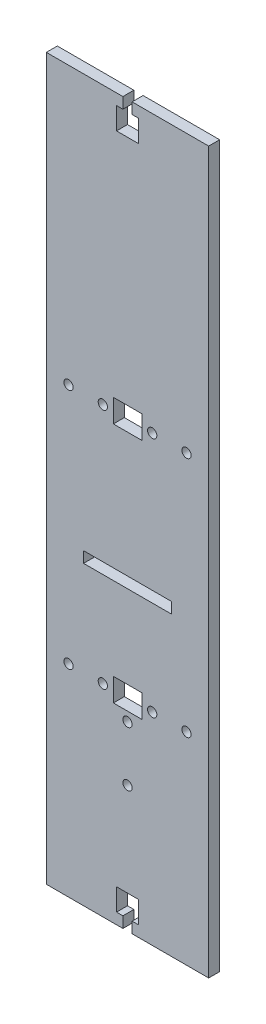
SolidWorks part; units mm, degrees
ref_plane "Front Plane" through (0, 0, 0) normal (0, 0, 1) x (1, 0, 0)
ref_plane "Top Plane" through (0, 0, 0) normal (0, 1, 0) x (1, 0, 0)
ref_plane "Right Plane" through (0, 0, 0) normal (1, 0, 0) x (0, 0, -1)
sketch "Sketch1" plane through (0, 0, 0) normal (0, 0, 1) x (1, 0, 0)
  line L1 (36.95, -164) -> (-36.95, -164)
  line L2 (36.95, -164) -> (36.95, 164)
  line L3 (36.95, 164) -> (-36.95, 164)
  line L4 (-36.95, -164) -> (-36.95, 164)
  line L5 (36.95, -164) -> (-36.95, 164) construction
  line L6 (36.95, 164) -> (-36.95, -164) construction
  point P0 (0, 0)
  dimension "D1" = 328
  dimension "D2" = 73.9
extrude "Boss-Extrude1" add sketch "Sketch1" along normal blind 5
sketch "Sketch2" plane through (0, 0, 5) normal (0, 0, 1) x (1, 0, 0)
  line L0 (-39.8376, -81.5) -> (39.8368, -81.5) construction
  line L1 (-39.8376, -84) -> (-39.8376, -79) construction
  line L2 (39.8368, -84) -> (39.8368, -79) construction
  circle A0 centre (-0.0004, -81.5) radius 2.1
  dimension "D1" = 4.2
extrude "Cut-Extrude1" cut sketch "Sketch2" against normal blind 10
sketch "Sketch3" plane through (0, 0, 5) normal (0, 0, 1) x (1, 0, 0)
  line L0 (36.95, 0) -> (15.9232, 0) construction
  line L1 (36.95, -164) -> (36.95, 164) construction
  line L2 (0, -164) -> (0, -137.9155) construction
  line L3 (-36.95, -164) -> (36.95, -164) construction
  line L4 (-2.1, -164) -> (-2.1, -159)
  line L5 (-2.1, -159) -> (-5, -159)
  line L6 (-5, -159) -> (-5, -149)
  line L7 (-5, -149) -> (5, -149)
  line L8 (-2.1, -164) -> (2.1, -164)
  line L9 (5, -159) -> (5, -149)
  line L10 (2.1, -159) -> (5, -159)
  line L11 (2.1, -164) -> (2.1, -159)
  line L12 (0, 164) -> (0, 137.9155) construction
  line L13 (2.1, 164) -> (2.1, 159)
  line L14 (2.1, 159) -> (5, 159)
  line L15 (5, 159) -> (5, 149)
  line L16 (-2.1, 164) -> (2.1, 164)
  line L17 (-5, 149) -> (5, 149)
  line L18 (-5, 159) -> (-5, 149)
  line L19 (-2.1, 159) -> (-5, 159)
  line L20 (-2.1, 164) -> (-2.1, 159)
  point P16 (0, -149)
  point P28 (0, 149)
  dimension "D1" = 4.2
  dimension "D2" = 10
  dimension "D3" = 10
  dimension "D4" = 5
extrude "Cut-Extrude2" cut sketch "Sketch3" against normal blind 10
sketch "Sketch5" plane through (0, 0, 5) normal (0, 0, 1) x (1, 0, 0)
  line L0 (-39.8376, -106.5) -> (39.8368, -106.5) construction
  line L1 (-39.8376, -109) -> (-39.8376, -104) construction
  line L2 (39.8368, -109) -> (39.8368, -104) construction
  circle A0 centre (-0.0004, -106.5) radius 2.1
  dimension "D1" = 4.2
extrude "Cut-Extrude3" cut sketch "Sketch5" against normal blind 5
sketch "Sketch6" plane through (0, 0, 5) normal (0, 0, 1) x (1, 0, 0)
  line L1 (-6.4404, 43.25) -> (6.5596, 43.25)
  line L2 (-6.4404, 43.25) -> (-6.4404, 32.75)
  line L3 (-6.4404, 32.75) -> (6.5596, 32.75)
  line L4 (6.5596, 43.25) -> (6.5596, 32.75)
  line L5 (-6.4404, 43.25) -> (6.5596, 32.75) construction
  line L6 (-6.4404, 32.75) -> (6.5596, 43.25) construction
  line L8 (19.8993, 43) -> (-19.9002, 43) construction
  line L9 (6.4396, 35) -> (6.4396, 41) construction
  line L10 (-0.0004, 73) -> (-0.0004, -107) construction
  line L11 (17.9996, 73) -> (-18.0004, 73) construction
  line L12 (-0.0004, -17) -> (12.0966, -17) construction
  line L13 (-6.4404, -66.75) -> (6.5596, -77.25) construction
  line L14 (-6.4404, -77.25) -> (6.5596, -66.75) construction
  line L15 (6.5596, -77.25) -> (6.5596, -66.75)
  line L16 (-6.4404, -66.75) -> (6.5596, -66.75)
  line L17 (-6.4404, -77.25) -> (-6.4404, -66.75)
  line L18 (-6.4404, -77.25) -> (6.5596, -77.25)
  circle A0 centre (-26.8566, 38) radius 2.1
  circle A1 centre (26.8557, 38) radius 2.1
  circle A2 centre (26.8557, -72) radius 2.1
  circle A3 centre (-26.8566, -72) radius 2.1
  point P4 (0.0596, 38)
  point P30 (0.0596, -72)
  dimension "D1" = 0.25
  dimension "D2" = 10.5
  dimension "D3" = 13
  dimension "D4" = 0.12
extrude "Cut-Extrude4" cut sketch "Sketch6" against normal blind 180
sketch "Sketch7" plane through (0, 0, 0) normal (0, 0, -1) x (-1, 0, 0)
  circle A0 centre (11.2504, 38) radius 2.1
  circle A1 centre (-11.2496, 38) radius 2.1
  circle A2 centre (-11.2496, -72) radius 2.1
  circle A3 centre (11.2504, -72) radius 2.1
extrude "Cut-Extrude5" cut sketch "Sketch7" against normal blind 180
sketch "Sketch8" plane through (0, 0, 5) normal (0, 0, 1) x (1, 0, 0)
  line L1 (-20.0004, -29) -> (19.9996, -29)
  line L2 (-20.0004, -29) -> (-20.0004, -24)
  line L3 (-20.0004, -24) -> (19.9996, -24)
  line L4 (19.9996, -29) -> (19.9996, -24)
extrude "Cut-Extrude6" cut sketch "Sketch8" against normal blind 5
